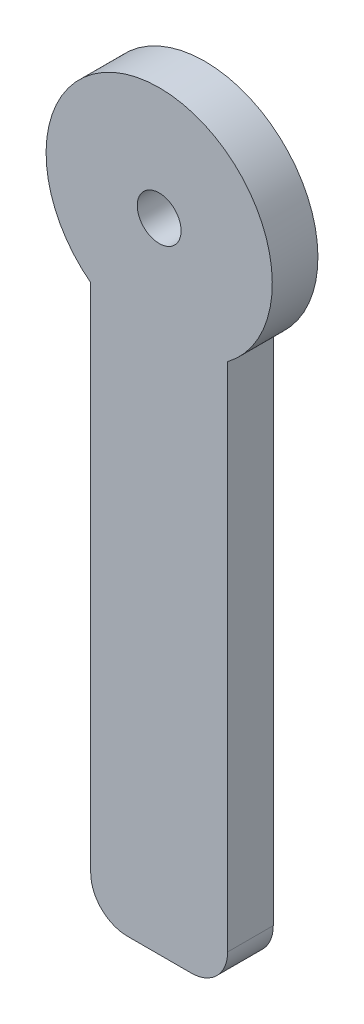
SolidWorks part; units mm, degrees
ref_plane "Front Plane" through (0, 0, 0) normal (0, 0, 1) x (1, 0, 0)
ref_plane "Top Plane" through (0, 0, 0) normal (0, 1, 0) x (1, 0, 0)
ref_plane "Right Plane" through (0, 0, 0) normal (1, 0, 0) x (0, 0, -1)
sketch "Sketch1" plane through (0, 0, 0) normal (0, 0, 1) x (1, 0, 0)
  line L0 (-2.54, 0) -> (-6.985, 0)
  line L1 (-9.525, 2.54) -> (-9.525, 38.1)
  line L2 (0, 2.54) -> (0, 38.1)
  arc A2 (-6.985, 0) -> (-9.525, 2.54) centre (-6.985, 2.54) cw
  arc A3 (-2.54, 0) -> (0, 2.54) centre (-2.54, 2.54) ccw
  arc A4 (-9.525, 38.1) -> (0, 38.1) centre (-4.7625, 44.363) cw
  point P6 (-4.7625, 52.231)
  point P12 (0, 0)
  dimension "D1" = 2.54
  dimension "D2" = 2.54
  dimension "D6" = 7.8681
  dimension "D3" = 38.1
  dimension "D4" = 38.1
  dimension "D5" = 9.525
extrude "Boss-Extrude1" add sketch "Sketch1" along normal blind 3.175
sketch "Sketch2" plane through (0, 0, 3.175) normal (0, 0, 1) x (1, 0, 0)
  circle A1 centre (-4.7625, 44.363) radius 1.524
  dimension "D1" = 3.048
extrude "Cut-Extrude1" cut sketch "Sketch2" against normal blind 3.175
